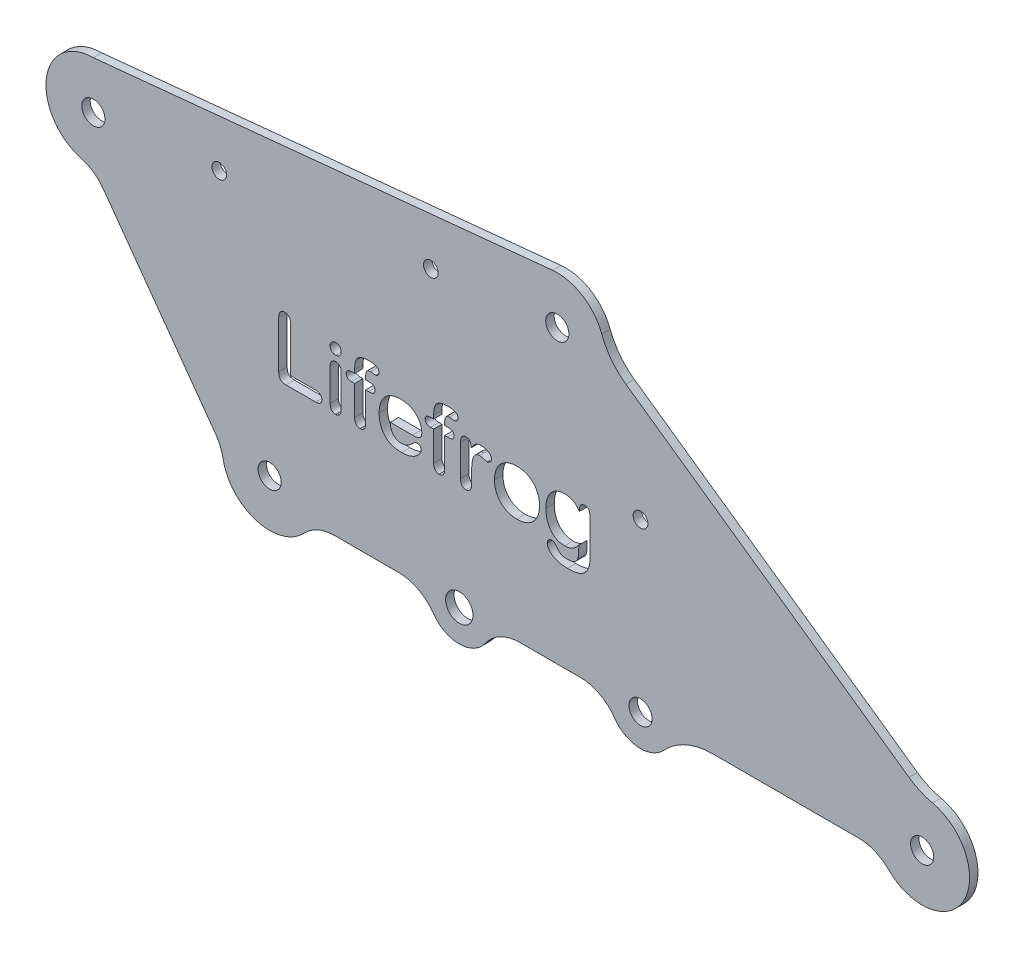
SolidWorks part; units mm, degrees
ref_plane "Front Plane" through (0, 0, 0) normal (0, 0, 1) x (1, 0, 0)
ref_plane "Top Plane" through (0, 0, 0) normal (0, 1, 0) x (1, 0, 0)
ref_plane "Right Plane" through (0, 0, 0) normal (1, 0, 0) x (0, 0, -1)
sketch "Sketch2" plane through (0, 0, 0) normal (0, 0, 1) x (1, 0, 0)
  line L0 (-96.303, -40.0195) -> (103.697, -40.0195) construction
  line L1 (56.1417, 22.4699) -> (-27.5885, 22.4699) construction
  line L2 (56.1417, 22.4699) -> (56.1417, -53.9544) construction
  line L3 (56.1417, -53.9544) -> (-159.2025, -53.9544) construction
  line L4 (-159.2025, 22.4699) -> (-159.2025, -53.9544) construction
  line L5 (-96.303, -40.0195) -> (-53.2713, -40.0195) construction
  line L6 (-100.4268, -47.0897) -> (-100.4268, -59.5897) construction
  line L7 (-100.4268, -59.5897) -> (73.7025, -59.5897) construction
  line L8 (-100.4268, -59.5897) -> (-302.9325, -59.5897) construction
  line L9 (-62.0853, -59.5897) -> (-73.2496, -62.9155) construction
  line L10 (-19.0853, -47.0897) -> (-16.3353, -47.0897) construction
  line L11 (47.7386, -47.0897) -> (47.7386, -41.2921) construction
  line L12 (-62.0853, -47.0897) -> (-107.0853, -47.0897) construction
  line L13 (-107.0853, -47.0897) -> (-107.0853, -42.5195) construction
  line L14 (-62.0853, -47.0897) -> (-58.8353, -47.0897) construction
  line L15 (-167.9726, 11.2199) -> (-124.5853, -42.5195) construction
  line L16 (-124.5853, -42.5195) -> (-167.9726, -37.8951) construction
  line L17 (-167.9726, -37.8951) -> (-167.9726, 11.2199) construction
  line L18 (-167.9726, -37.8951) -> (-167.9726, -59.5897) construction
  line L19 (-146.4823, -3.4151) -> (-119.9002, -40.3454)
  line L21 (-148.9187, 22.4699) -> (-39.9417, 33.2746)
  line L24 (-22.5647, 18.5545) -> (44.5996, -28.6343)
  line L25 (11.3122, -40.0195) -> (103.697, -40.0195) construction
  line L26 (-41.384, 22.4699) -> (-159.2025, 22.4699) construction
  line L27 (-47.7239, -47.0897) -> (-33.4467, -47.0897)
  line L28 (-1.9905, -47.0897) -> (32.6866, -47.0897)
  line L29 (-76.4467, -47.0897) -> (-91.6169, -47.0897)
  line L30 (-54.5853, -47.0897) -> (-19.0853, -47.0897) construction
  line L31 (-11.5853, -47.0897) -> (47.7386, -47.0897) construction
  line L32 (-148.9187, 11.2199) -> (-38.8318, 22.0795) construction
  arc A0 (-26.3612, 21.2219) -> (-51.3257, 22.4699) centre (-38.8318, 22.0795) ccw construction
  circle A1 centre (-38.8318, 22.0795) radius 2.75 construction
  arc A2 (-74.5853, -47.0897) -> (-51.639, -53.9544) centre (-62.0853, -47.0897) ccw construction
  circle A3 centre (-62.0853, -47.0897) radius 3.25 construction
  circle A4 centre (47.7386, -42.0897) radius 2.75
  circle A5 centre (-19.0853, -47.0897) radius 2.75 construction
  circle A6 centre (47.7386, -42.0897) radius 17.5 construction
  circle A7 centre (47.7386, -42.0897) radius 2.75 construction
  circle A8 centre (-107.0853, -42.5195) radius 17.5 construction
  circle A9 centre (-107.0853, -42.5195) radius 2.75 construction
  circle A10 centre (-148.9187, 11.2199) radius 19.0539 construction
  circle A11 centre (-148.9187, 11.2199) radius 2.75 construction
  arc A12 (-148.9187, 22.4699) -> (-151.9256, 0.3791) centre (-148.9187, 11.2199) ccw
  arc A13 (-118.1664, -44.4613) -> (-98.8961, -50.2332) centre (-107.0853, -42.5195) ccw
  arc A14 (-28.2784, 25.9769) -> (-39.9417, 33.2746) centre (-38.8318, 22.0795) ccw
  arc A15 (-68.2402, -51.3754) -> (-55.9304, -51.3754) centre (-62.0853, -47.0897) ccw
  arc A16 (-25.2402, -51.3754) -> (-13.5666, -52.1685) centre (-19.0853, -47.0897) ccw
  arc A17 (39.7699, -50.0309) -> (50.2007, -31.1125) centre (47.7386, -42.0897) ccw
  arc A18 (-7.7098, -42.5525) -> (-9.0853, -40.0195) centre (-19.0853, -47.0897) ccw construction
  arc A19 (-31.8119, -47.0897) -> (-8.3689, -53.9544) centre (-19.0853, -47.0897) ccw construction
  circle A20 centre (-19.0853, -47.0897) radius 2.75
  circle A21 centre (-62.0853, -47.0897) radius 3.25
  circle A22 centre (-107.0853, -42.5195) radius 2.75
  circle A23 centre (-148.9187, 11.2199) radius 2.75
  circle A24 centre (-38.8318, 22.0795) radius 2.75
  arc A25 (32.6866, -47.0897) -> (39.7699, -50.0309) centre (32.6866, -57.0897) cw
  arc A26 (-146.4823, -3.4151) -> (-151.9256, 0.3791) centre (-154.5984, -9.257) ccw
  arc A27 (-119.9002, -40.3454) -> (-118.1664, -44.4613) centre (-128.0164, -46.1873) cw
  arc A28 (-91.6169, -47.0897) -> (-98.8961, -50.2332) centre (-91.6169, -57.0897) ccw
  arc A29 (-76.4467, -47.0897) -> (-68.2402, -51.3754) centre (-76.4467, -57.0897) cw
  arc A30 (-33.4467, -47.0897) -> (-25.2402, -51.3754) centre (-33.4467, -57.0897) cw
  arc A31 (-47.7239, -47.0897) -> (-55.9304, -51.3754) centre (-47.7239, -57.0897) ccw
  arc A33 (-22.5647, 18.5545) -> (-28.2784, 25.9769) centre (-13.5206, 31.4271) cw
  arc A34 (44.5996, -28.6343) -> (50.2007, -31.1125) centre (53.6437, -15.7617) ccw
  arc A35 (-1.9905, -47.0897) -> (-13.5666, -52.1685) centre (-1.9905, -62.8218) ccw
  point P67 (37.6608, -47.0897)
  point P70 (-148.9187, -0.0301)
  point P73 (-118.3353, -42.5195)
  point P76 (-96.8054, -47.0897)
  point P79 (-69.5853, -47.0897)
  point P82 (-26.5853, -47.0897)
  point P91 (-27.5818, 22.0795)
  point P94 (47.7386, -30.8397)
  dimension "D1" = 25
  dimension "D2" = 5.5
  dimension "D5" = 35
  dimension "D6" = 5.5
  dimension "D10" = 22.5
  dimension "D11" = 22.5
  dimension "D12" = 22.5
  dimension "D13" = 5.5
  dimension "D14" = 5.5
  dimension "D15" = 15
  dimension "D16" = 15
  dimension "D17" = 22.5
  dimension "D18" = 10
  dimension "D19" = 5.5
  dimension "D3" = 20
  dimension "D4" = 0
  dimension "D7" = 45
  dimension "D8" = 43
  dimension "D9" = 45
extrude "Boss-Extrude1" add sketch "Sketch2" along normal blind 2
sketch "Sketch5" plane through (0, 0, 2) normal (0, 0, 1) x (1, 0, 0)
  line L1 (-106.4284, -21.9146) -> (-30.7738, -21.9146) construction
  line L2 (-106.4284, -21.9146) -> (-106.4284, -6.1743) construction
  line L3 (-106.4284, -6.1743) -> (-30.7738, -6.1743) construction
  line L4 (-30.7738, -21.9146) -> (-30.7738, -6.1743) construction
  text T0 "Lifefrog" font "Arial Rounded MT Bold" height 15
sketch "Sketch7" plane through (0, 0, 2) normal (0, 0, 1) x (1, 0, 0)
  line L0 (-148.9187, 11.2199) -> (-38.8318, 22.0795) construction
  line L1 (-148.9187, 11.2199) -> (-107.0853, -42.5195) construction
  line L2 (-107.0853, -42.5195) -> (25.9147, -42.5195) construction
  line L3 (25.9147, -42.5195) -> (-38.8318, 22.0795) construction
  line L5 (-107.0853, -2.5195) -> (-35.0853, -2.5195) construction
  line L6 (25.9147, -42.5195) -> (25.9147, -7.5195) construction
  line L7 (25.9147, -7.5195) -> (-64.0853, -7.5195) construction
  circle A0 centre (-119.0636, 14.1649) radius 1.75
  circle A1 centre (-68.8318, 19.1201) radius 1.75
  circle A5 centre (-19.0853, -7.5195) radius 1.75
  dimension "D1" = 3.5
  dimension "D2" = 3.5
  dimension "D4" = 30
  dimension "D5" = 3.5
  dimension "D6" = 40
  dimension "D3" = 30
  dimension "D7" = 35
  dimension "D9" = 45
extrude "Cut-Extrude4" cut sketch "Sketch7" against normal through all
extrude "Cut-Extrude5" cut sketch "Sketch5" against normal blind 10
sketch "Sketch8" plane through (0, 0, 2) normal (0, 0, 1) x (1, 0, 0)
  line L0 (-77.3813, -14.5454) -> (-75.1653, -14.5454) construction
  line L1 (-77.3813, -12.2092) -> (-75.1653, -12.2092)
  line L2 (-77.3813, -16.8816) -> (-75.1653, -16.8816)
  arc A0 (-77.3813, -12.2092) -> (-77.3813, -16.8816) centre (-77.3813, -14.5454) ccw
  arc A1 (-75.1653, -16.8816) -> (-75.1653, -12.2092) centre (-75.1653, -14.5454) ccw
  circle A2 centre (-48.7434, -16.6446) radius 4.4437
  circle A3 centre (-36.9422, -16.6446) radius 3.9871
  point P2 (-76.2733, -14.5454)
extrude "Cut-Extrude6" cut sketch "Sketch8" against normal blind 10
